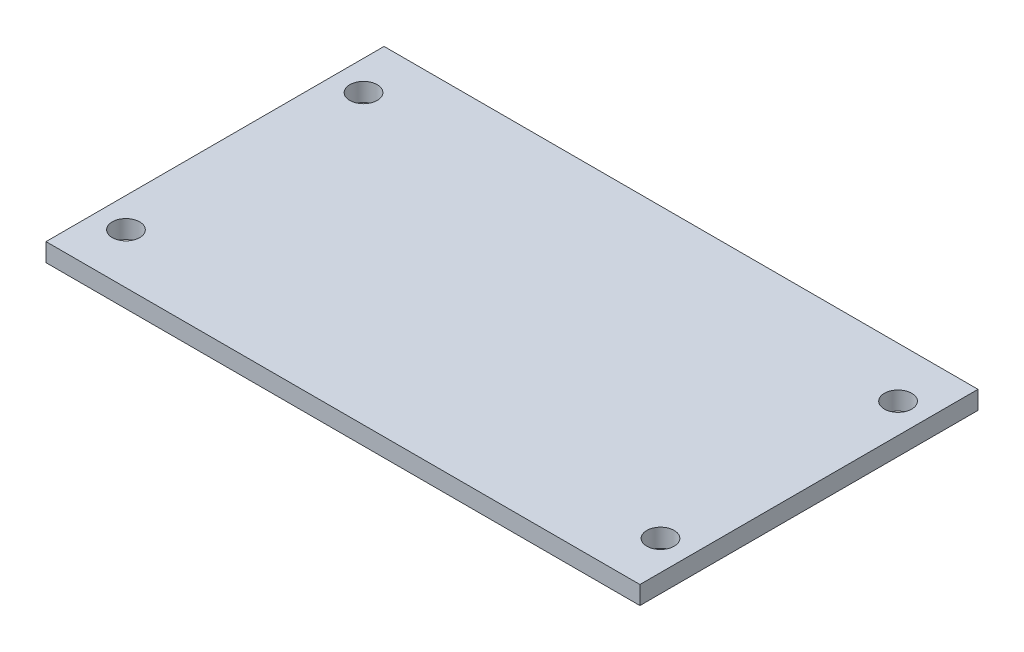
SolidWorks part; units mm, degrees
ref_plane "Płaszczyzna przednia" through (0, 0, 0) normal (0, 0, 1) x (1, 0, 0)
ref_plane "Płaszczyzna górna" through (0, 0, 0) normal (0, 1, 0) x (1, 0, 0)
ref_plane "Płaszczyzna prawa" through (0, 0, 0) normal (1, 0, 0) x (0, 0, -1)
sketch "Sketch2" plane through (0, 0, 0) normal (0, 0, 1) x (1, 0, 0)
  line L0 (0, 0) -> (17.5, 0) construction
  line L5 (0, 0) -> (-17.5, 0) construction
  line L7 (-17.5, 0) -> (-17.5, -1) construction
  line L8 (17.5, 0) -> (17.5, -1) construction
  line L9 (17.5, -1) -> (13.5, -1) construction
  line L10 (13.5, -1) -> (13.5, -7.5) construction
  line L11 (-17.5, -1) -> (-13.5, -1) construction
  line L12 (-13.5, -1) -> (-13.5, -7.5) construction
  line L13 (-13.5, -7.5) -> (13.5, -7.5) construction
  line L14 (-17.5, 0) -> (-17.5, -1) construction
  line L15 (-17.5, 0) -> (-17.5, -1)
  line L16 (-17.5, -1) -> (-14.5, -1)
  line L17 (-14.5, -1) -> (-14.5, -5)
  line L18 (-14.5, -5) -> (-22.5, -5)
  line L19 (-22.5, -5) -> (-22.5, 0)
  line L20 (-22.5, 0) -> (-22.5, 4)
  line L21 (-22.5, 4) -> (22.5, 4)
  line L22 (22.5, 4) -> (22.5, -5)
  line L23 (22.5, -5) -> (14.5, -5)
  line L24 (14.5, -5) -> (14.5, -1)
  line L25 (14.5, -1) -> (17.5, -1)
  line L26 (17.5, -1) -> (17.5, 0)
  line L27 (17.5, 0) -> (-17.5, 0)
  point P10 (-22.5, 0)
  point P11 (-22.5, -5)
  point P12 (-14.5, -5)
  point P13 (-22.5, 0)
  point P14 (-22.5, 4)
  point P16 (-14.5, -1)
  point P17 (-17.5, -1)
  point P18 (-17.5, 0)
  dimension "D1" = 5
  dimension "D2" = 5
  dimension "D3" = 8
  dimension "D4" = 4
  dimension "D5" = 0
  dimension "D6" = 0
  dimension "D7" = 35
  dimension "D8" = 1
  dimension "D9" = 4
  dimension "D10" = 4
  dimension "D11" = 1
  dimension "D12" = 27
  dimension "D13" = 6.5
  dimension "D14" = 6.5
  dimension "D16" = 3
  dimension "D17" = 1
  dimension "D18" = 9
  dimension "D19" = 9
  dimension "D20" = 8
  dimension "D21" = 1
  dimension "D22" = 0
  dimension "D23" = 0
  dimension "D25" = 45
extrude "Boss-Extrude1" add sketch "Sketch2" along normal blind 10
sketch "Sketch3" plane through (0, 4, 0) normal (0, 1, 0) x (1, 0, 0)
  line L0 (22.5, 0) -> (-22.5, 0) construction
  line L1 (-22.5, -10) -> (-22.5, 0) construction
  line L3 (32.5, -23.5) -> (-32.5, -23.5)
  line L4 (32.5, -23.5) -> (32.5, 13.5)
  line L5 (32.5, 13.5) -> (-32.5, 13.5)
  line L6 (-32.5, -23.5) -> (-32.5, 13.5)
  line L7 (32.5, -23.5) -> (-32.5, 13.5) construction
  line L8 (32.5, 13.5) -> (-32.5, -23.5) construction
  point P0 (0, -5)
  point P5 (0, -5)
  dimension "D1" = 5
  dimension "D2" = 22.5
  dimension "D3" = 37
  dimension "D4" = 65
extrude "Boss-Extrude2" add sketch "Sketch3" along normal blind 2
sketch "Sketch4" plane through (0, 6, 0) normal (0, 1, 0) x (1, 0, 0)
  line L0 (-32.5, -23.5) -> (32.5, -23.5) construction
  line L1 (-32.5, 13.5) -> (-32.5, -23.5) construction
  line L3 (-29.25, -18) -> (29.25, -18) construction
  line L4 (-29.25, -18) -> (-29.25, 8) construction
  line L5 (-29.25, 8) -> (29.25, 8) construction
  line L6 (29.25, -18) -> (29.25, 8) construction
  line L7 (-29.25, -18) -> (29.25, 8) construction
  line L8 (-29.25, 8) -> (29.25, -18) construction
  circle A0 centre (-29.25, 8) radius 1.5
  circle A1 centre (-29.25, -18) radius 1.5
  circle A2 centre (29.25, -18) radius 1.5
  circle A3 centre (29.25, 8) radius 1.5
  point P0 (0, -5)
  point P5 (0, -5)
  dimension "D1" = 18.5
  dimension "D2" = 32.5
  dimension "D3" = 26
  dimension "D4" = 58.5
extrude "Cut-Extrude1" cut sketch "Sketch4" against normal blind 5
